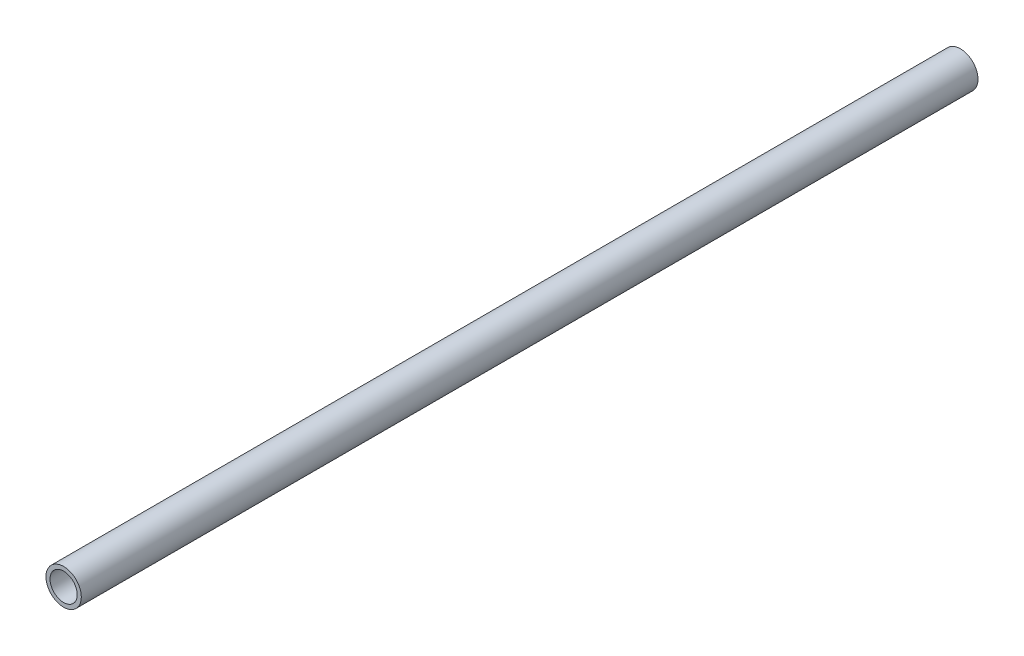
SolidWorks part; units mm, degrees
material "3.0255 (EN-AW 1350A)"
ref_plane "Alzado" through (0, 0, 0) normal (0, 0, 1) x (1, 0, 0)
ref_plane "Planta" through (0, 0, 0) normal (0, 1, 0) x (1, 0, 0)
ref_plane "Vista lateral" through (0, 0, 0) normal (1, 0, 0) x (0, 0, -1)
sketch "Croquis1" plane through (0, 0, 0) normal (0, 0, 1) x (1, 0, 0)
  circle A0 centre (0, 0) radius 5
  circle A1 centre (0, 0) radius 6.5
  dimension "D1" = 13
  dimension "D2" = 1.5
extrude "Saliente-Extruir1" add sketch "Croquis1" along normal mid plane 330
